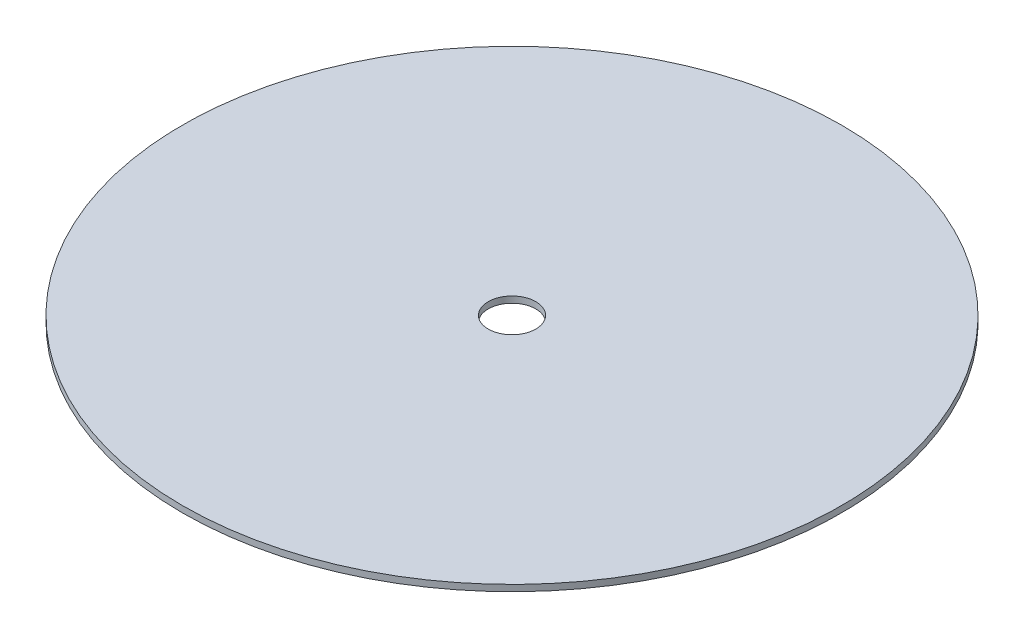
SolidWorks part; units mm, degrees
material "Thornel Mat VMA"
ref_plane "Front Plane" through (0, 0, 0) normal (0, 0, 1) x (1, 0, 0)
ref_plane "Top Plane" through (0, 0, 0) normal (0, 1, 0) x (1, 0, 0)
ref_plane "Right Plane" through (0, 0, 0) normal (1, 0, 0) x (0, 0, -1)
sketch "Sketch1" plane through (0, 0, 0) normal (0, 1, 0) x (1, 0, 0)
  circle A0 centre (0, 0) radius 66.04
  circle A1 centre (0, 0) radius 4.7625
  dimension "D1" = 132.08
  dimension "D2" = 9.525
extrude "Boss-Extrude1" add sketch "Sketch1" along normal blind 1.27
